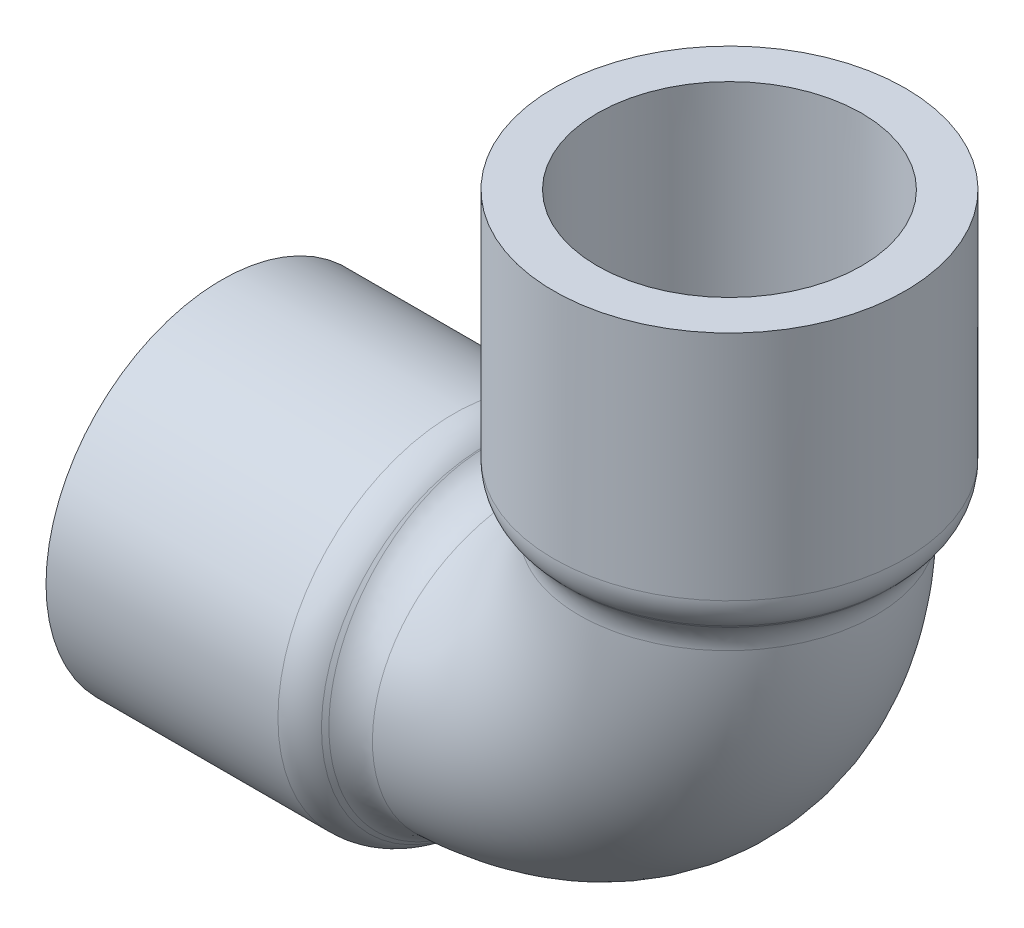
SolidWorks part; units mm, degrees
ref_plane "Front Plane" through (0, 0, 0) normal (0, 0, 1) x (1, 0, 0)
ref_plane "Top Plane" through (0, 0, 0) normal (0, 1, 0) x (1, 0, 0)
ref_plane "Right Plane" through (0, 0, 0) normal (1, 0, 0) x (0, 0, -1)
sketch "Sketch0" plane through (0, 0, 0) normal (0, 0, 1) x (1, 0, 0)
  line L0 (-51.5938, 0) -> (0, 0) construction
  line L1 (0, 0) -> (0, 51.5938) construction
  line L2 (-26.1938, 0) -> (0, 0) construction
  line L3 (0, 0) -> (0, 26.1938) construction
  line L4 (-51.5937, 17.8594) -> (-51.5937, -17.8594) construction
  line L5 (-26.1937, 13.2842) -> (-51.5937, 13.4366) construction
  line L6 (-26.1937, 13.2842) -> (-26.1937, -13.2842) construction
  line L7 (-26.1937, -13.2842) -> (-51.5937, -13.4366) construction
  line L8 (-51.5937, 13.4366) -> (-51.5937, -13.4366) construction
  line L9 (-17.8594, 51.5938) -> (17.8594, 51.5938) construction
  line L10 (-13.4366, 51.5938) -> (13.4366, 51.5938) construction
  line L11 (13.4366, 51.5938) -> (13.2842, 26.1938) construction
  line L12 (13.2842, 26.1938) -> (-13.2842, 26.1938) construction
  line L13 (-13.2842, 26.1938) -> (-13.4366, 51.5938) construction
  line L14 (-26.1937, 10.4648) -> (-26.1937, -10.4648) construction
  line L15 (-26.1937, -10.4648) -> (-26.1937, -14.8876) construction
  line L16 (-51.5937, -13.4366) -> (-51.5937, -17.8594) construction
  line L17 (10.4648, 26.1938) -> (14.8876, 26.1938) construction
  line L18 (-10.4648, 26.1938) -> (10.4648, 26.1938) construction
  line L19 (13.4366, 51.5938) -> (17.8594, 51.5938) construction
  dimension "D1" = 4.4228
  dimension "H" = 51.5938
  dimension "G" = 26.1937
  dimension "M" = 35.7188
  dimension "OD A" = 26.8732
  dimension "OD B" = 26.5684
  dimension "ID" = 20.9296
sketch "Sketch1" plane through (0, 0, 0) normal (0, 0, 1) x (1, 0, 0)
  line L0 (-51.5938, 0) -> (0, 0) construction
  line L1 (-51.5938, 0) -> (0, 0) construction
  line L2 (-26.1937, -17.8594) -> (-23.2219, -14.8876)
  line L3 (-51.5937, -17.8594) -> (-26.1937, -17.8594)
  line L4 (-51.5937, -17.8594) -> (-51.5937, -13.4366)
  line L5 (-51.5937, -13.4366) -> (-26.1937, -13.2842)
  line L6 (-26.1937, -17.8594) -> (-26.1937, -13.2842) construction
  line L7 (-23.2219, -14.8876) -> (-23.2219, -10.4648)
  line L8 (-23.2219, -10.4648) -> (-26.1937, -13.2842)
  line L9 (-26.1937, -17.8594) -> (-23.2219, -17.8594) construction
  line L10 (-26.1937, -10.4648) -> (-23.2219, -10.4648) construction
  line L11 (-23.2219, -17.8594) -> (-23.2219, -14.8876) construction
  line L12 (-26.1937, -14.8876) -> (-23.2219, -14.8876) construction
revolve "Revolve1" add sketch "Sketch1" angle 360 about L1
sketch "Sketch2" plane through (0, 0, 0) normal (0, 0, 1) x (1, 0, 0)
  line L0 (13.4366, 51.5938) -> (13.2842, 26.1938)
  line L1 (13.2842, 26.1938) -> (17.8594, 26.1937) construction
  line L2 (17.8594, 26.1937) -> (17.8594, 51.5938)
  line L3 (17.8594, 51.5938) -> (13.4366, 51.5938)
  line L4 (0, 0) -> (0, 51.5938) construction
  line L5 (0, 0) -> (0, 51.5938) construction
  line L6 (13.2842, 26.1938) -> (10.4648, 23.2219)
  line L7 (10.4648, 26.1938) -> (10.4648, 23.2219) construction
  line L8 (17.8594, 26.1937) -> (14.8876, 23.2219)
  line L9 (14.8876, 23.2219) -> (10.4648, 23.2219)
  line L10 (17.8594, 26.1937) -> (17.8594, 23.2219) construction
  line L11 (17.8594, 23.2219) -> (14.8876, 23.2219) construction
  line L12 (14.8876, 26.1938) -> (14.8876, 23.2219) construction
revolve "Revolve2" add sketch "Sketch2" angle 360 about L5
sketch "Sketch3" plane through (-23.2219, 0, 0) normal (1, 0, 0) x (0, 0, -1)
  circle A0 centre (0, 0) radius 10.4648
  circle A1 centre (0, 0) radius 14.8876
sketch "Sketch4" plane through (0, 0, 0) normal (0, 0, 1) x (1, 0, 0)
  line L0 (-51.5938, 0) -> (0, 0) construction
  line L1 (0, 0) -> (0, 51.5938) construction
  line L2 (-51.5938, 0) -> (-23.2219, 0) construction
  line L3 (0, 23.2219) -> (0, 51.5938) construction
  line L4 (-23.2219, -14.8876) -> (-23.2219, 14.8876) construction
  arc A0 (-23.2219, 0) -> (0, 23.2219) centre (-23.2219, 23.2219) ccw
sweep "Sweep1" add profiles "Sketch3" path "Sketch4"
fillet "Fillet1" radius 4.4228 4 edges at (-23.2219, 0, -14.8876) (0, 23.2219, -14.8876) (0, 26.1937, -17.8594) (-26.1937, 0, 17.8594)
equation "\"D1@Fillet1\" = \"D1@Sketch0\""
